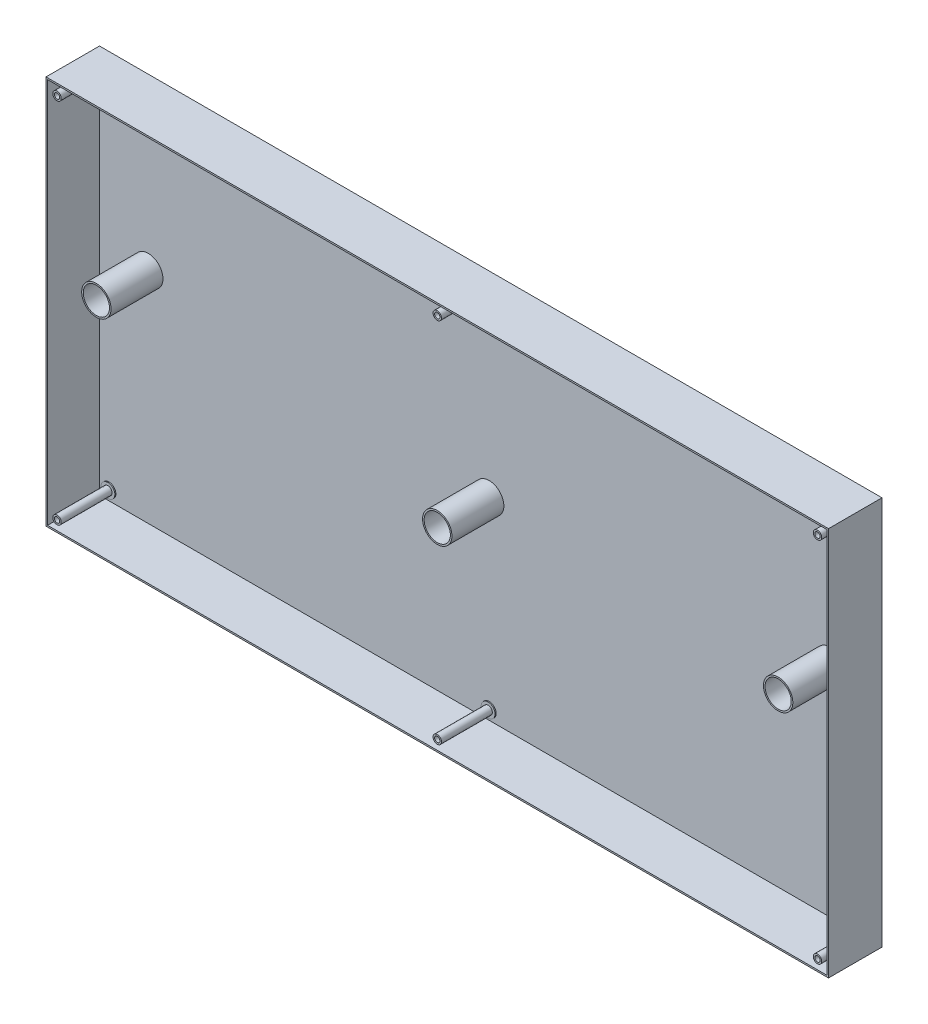
SolidWorks part; units mm, degrees
material "Thornel Mat VMA"
ref_plane "Front" through (0, 0, 0) normal (0, 0, 1) x (1, 0, 0)
ref_plane "Top" through (0, 0, 0) normal (0, 1, 0) x (1, 0, 0)
ref_plane "Right" through (0, 0, 0) normal (1, 0, 0) x (0, 0, -1)
ref_plane "Plane1" through (0, 0, 102) normal (0, 0, 1) x (1, 0, 0)
sketch "Sketch1" plane through (0, 0, 102) normal (0, 0, 1) x (1, 0, 0)
  line L0 (746, -371) -> (746, 371)
  line L1 (746, 371) -> (-746, 371)
  line L2 (-746, 371) -> (-746, -371)
  line L3 (-746, -371) -> (746, -371)
extrude "Boss-Extrude1" add sketch "Sketch1" against normal blind 102
hole_wizard "Hole1" positions "Sketch3" profile "Sketch2" legacy
sketch "Sketch3" plane through (0, 0, 0) normal (0, 0, -1) x (-1, 0, 0)
  point P0 (725, 350)
  point P1 (-725, 350)
  point P2 (-725, -350)
  point P3 (725, -350)
  point P4 (0, 350)
  point P5 (0, -350)
sketch "Sketch2" plane through (-725, 350, 0) normal (1, 0, 0) x (0, 1, 0)
  line L0 (0, 0) -> (0, 102)
  line L1 (0, 102) -> (5.05, 102)
  line L2 (5.05, 102) -> (5.05, 2)
  line L3 (5.05, 2) -> (10.25, 2)
  line L4 (10.25, 2) -> (10.25, 0)
  line L5 (10.25, 0) -> (0, 0)
  line L6 (0, 110) -> (0, -10) construction
  dimension "Diameter" = 10.1
  dimension "Depth" = 102
  dimension "C-Bore Diameter" = 20.5
  dimension "C-Bore Depth" = 2
hole_wizard "M45 Clearance Hole1" positions "Sketch5" profile "Sketch4" hole size "M45" standard "ANSI Metric"
sketch "Sketch5" plane through (0, 0, 102) normal (0, 0, 1) x (1, 0, 0)
  point P0 (650, 50)
  point P1 (0, 0)
  point P2 (-650, 50)
sketch "Sketch4" plane through (650, 50, 102) normal (1, 0, 0) x (0, -1, 0)
  line L0 (0, 0) -> (0, 102)
  line L1 (0, 102) -> (25, 102)
  line L2 (25, 102) -> (25, 0)
  line L5 (25, 0) -> (0, 0)
  line L11 (0, -6.35) -> (0, 107.95) construction
  dimension "Thru Hole Dia." = 50
  dimension "Thru Hole Depth" = 102
shell "Shell1" thickness 3
